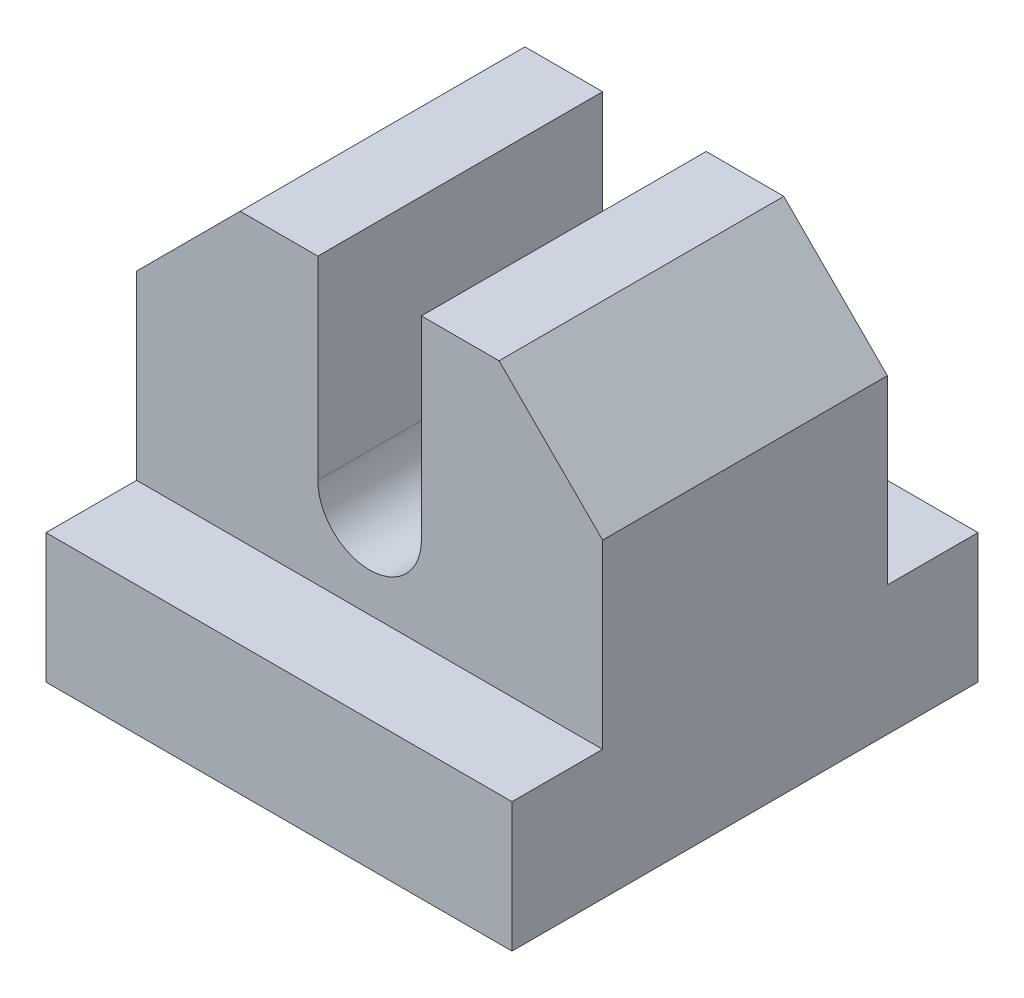
SolidWorks part; units mm, degrees
material "Aluminum Bronze"
ref_plane "Front Plane" through (0, 0, 0) normal (0, 0, 1) x (1, 0, 0)
ref_plane "Top Plane" through (0, 0, 0) normal (0, 1, 0) x (1, 0, 0)
ref_plane "Right Plane" through (0, 0, 0) normal (1, 0, 0) x (0, 0, -1)
sketch "Sketch1" plane through (0, 0, 0) normal (0, 1, 0) x (1, 0, 0)
  line L1 (-268.2, 380.7) -> (-250.2, 380.7)
  line L2 (-268.2, 380.7) -> (-268.2, 362.7)
  line L3 (-268.2, 362.7) -> (-250.2, 362.7)
  line L4 (-250.2, 380.7) -> (-250.2, 362.7)
  dimension "D1" = 18
  dimension "D2" = 18
extrude "Boss-Extrude1" add sketch "Sketch1" along normal blind 5
sketch "Sketch4" plane through (0, 0, 0) normal (0, -1, 0) x (1, 0, 0)
  line L0 (-250.2, -362.7) -> (-250.2, -380.7) construction
  line L1 (-268.2, -380.7) -> (-268.2, -362.7) construction
  line L2 (-253.2, -377.7) -> (-265.2, -377.7)
  line L3 (-253.2, -377.7) -> (-253.2, -365.7)
  line L4 (-253.2, -365.7) -> (-265.2, -365.7)
  line L5 (-265.2, -377.7) -> (-265.2, -365.7)
  line L6 (-268.2, -362.7) -> (-250.2, -362.7) construction
  line L7 (-250.2, -380.7) -> (-268.2, -380.7) construction
  point P6 (0, 0)
  dimension "D1" = 3
  dimension "D2" = 3
  dimension "D3" = 3
  dimension "D4" = 3
extrude "Cut-Extrude1" cut sketch "Sketch4" against normal blind 3
sketch "Sketch5" plane through (0, 5, 0) normal (0, 1, 0) x (1, 0, 0)
  line L0 (-250.2, 380.7) -> (-268.2, 380.7) construction
  line L1 (-268.2, 377.2) -> (-250.2, 377.2)
  line L2 (-268.2, 377.2) -> (-268.2, 366.2)
  line L3 (-268.2, 366.2) -> (-250.2, 366.2)
  line L4 (-250.2, 377.2) -> (-250.2, 366.2)
  line L5 (-268.2, 362.7) -> (-250.2, 362.7) construction
  dimension "D1" = 3.5
  dimension "D2" = 3.5
extrude "Boss-Extrude2" add sketch "Sketch5" along normal blind 11
sketch "Sketch7" plane through (0, 0, -366.2) normal (0, 0, 1) x (1, 0, 0)
  line L0 (-259.2, 16) -> (-257.2, 16)
  line L1 (-268.2, 16) -> (-250.2, 16) construction
  line L2 (-259.2, 16) -> (-261.2, 16)
  line L3 (-268.2, 0) -> (-250.2, 0) construction
  line L4 (-261.2, 16) -> (-257.2, 16)
  line L5 (-261.2, 16) -> (-261.2, 8.5)
  line L6 (-261.2, 8.5) -> (-257.2, 8.5)
  line L7 (-257.2, 16) -> (-257.2, 8.5)
  line L8 (-259.2, 16) -> (-254.2, 16)
  line L9 (-254.2, 16) -> (-248.8377, 10.6377)
  line L10 (-264.2, 16) -> (-268.2, 12)
  line L11 (-268.2, 16) -> (-268.2, 5) construction
  line L12 (-264.2, 16) -> (-268.2, 16)
  line L13 (-268.2, 16) -> (-268.2, 12)
  line L14 (-254.2, 16) -> (-250.2, 16)
  line L15 (-250.2, 16) -> (-250.2, 12)
  line L16 (-250.2, 16) -> (-250.2, 5) construction
  circle A0 centre (-259.2, 8.5) radius 2
  line M8 (-250.2, 5) -> (-250.2, 16)
  line M9 (-250.2, 16) -> (-268.2, 16)
  line M10 (-268.2, 16) -> (-268.2, 5)
  dimension "D1" = 2
  dimension "D2" = 2
  dimension "D3" = 8.5
  dimension "D4" = 5
  dimension "D5" = 45
  dimension "D6" = 3
  dimension "D7" = 45
extrude "Cut-Extrude2" cut sketch "Sketch7" against normal through all contours L6 A0 | L6 A0 | A0 L7 L5 M9 | L9 M9 M8 | L10 M9 M10
